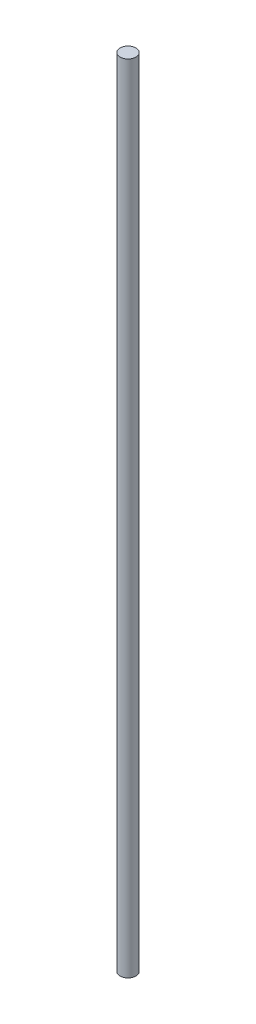
SolidWorks part; units mm, degrees
material "AISI 1035 钢 (SS)"
ref_plane "前视基准面" through (0, 0, 0) normal (0, 0, 1) x (1, 0, 0)
ref_plane "上视基准面" through (0, 0, 0) normal (0, 1, 0) x (1, 0, 0)
ref_plane "右视基准面" through (0, 0, 0) normal (1, 0, 0) x (0, 0, -1)
sketch "草图1" plane through (0, 0, 0) normal (0, 1, 0) x (1, 0, 0)
  circle A0 centre (0, 0) radius 4
  dimension "D1" = 8
extrude "凸台-拉伸1" add sketch "草图1" along normal blind 400
